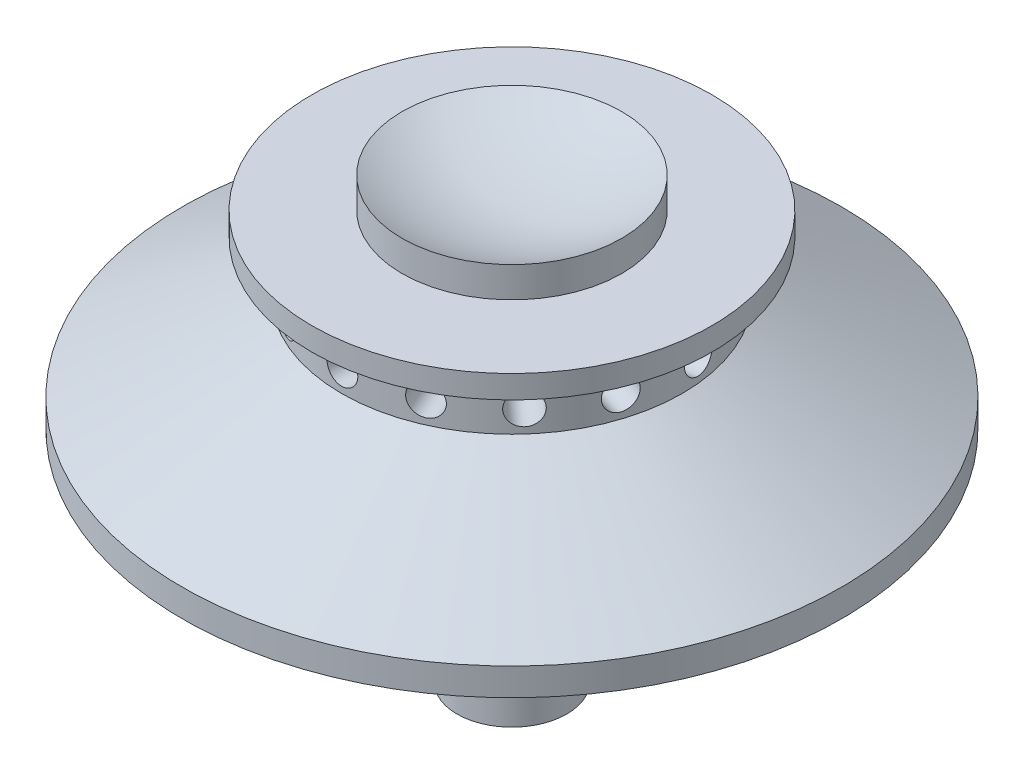
SolidWorks part; units mm, degrees
material "3003 Alloy"
ref_plane "Front Plane" through (0, 0, 0) normal (0, 0, 1) x (1, 0, 0)
ref_plane "Top Plane" through (0, 0, 0) normal (0, 1, 0) x (1, 0, 0)
ref_plane "Right Plane" through (0, 0, 0) normal (1, 0, 0) x (0, 0, -1)
sketch "Sketch1" plane through (0, 0, 0) normal (0, 0, 1) x (1, 0, 0)
  line L0 (0, 0) -> (-38.1, 0)
  line L1 (-38.1, 0) -> (-38.1, 3.175)
  line L2 (0, 0) -> (0, 22.225)
  line L3 (-12.7, 21.8741) -> (-12.7, 25.4)
  line L4 (-12.7, 21.8741) -> (-23.1308, 21.8741)
  line L5 (-23.1308, 21.8741) -> (-23.1308, 19.2253)
  line L6 (-23.1308, 19.2253) -> (-19.683, 19.2253)
  line L7 (-19.683, 19.2253) -> (-19.683, 13.3554)
  line L8 (-19.683, 13.3554) -> (-38.1, 3.175)
  line L9 (0, 22.225) -> (13.4343, 22.225) construction
  line L10 (0, 22.225) -> (0, 49.2125) construction
  arc A0 (0, 22.225) -> (-12.7, 25.4) centre (0, 49.2125) cw
  dimension "D6" = 22.225
  dimension "D1" = 76.2
  dimension "D4" = 25.4
  dimension "D5" = 3.175
  dimension "D7" = 25.4
revolve "Revolve1" add sketch "Sketch1" angle 360 about L10
hole_wizard "9/64 (0.14063) Diameter Hole1" positions "3DSketch1" profile "Sketch2" hole size "9/64" standard "Ansi Inch"
sketch3d "3DSketch1"
  point P0 (0, 15.875, 19.683)
  dimension "D1" = 15.875
sketch "Sketch2" plane through (0, 15.875, 19.683) normal (1, 0, 0) x (0, -1, 0)
  line L0 (0, 0) -> (0, 13.7731)
  line L1 (0, 13.7731) -> (1.786, 12.7)
  line L2 (1.786, 12.7) -> (1.786, 0)
  line L5 (1.786, 0) -> (0, 0)
  line L10 (0, 13.7731) -> (-1.786, 12.7) construction
  line L11 (0, -6.35) -> (0, 107.95) construction
  dimension "Hole Dia." = 3.572
  dimension "Hole Depth" = 12.7
  dimension "Drill Angle" = 118
pattern_circular "CirPattern1" count 15 over 360 about axis through (0, 22.225, 0) along (0, 1, 0) of "9/64 (0.14063) Diameter Hole1"
sketch "Sketch3" plane through (0, 0, 0) normal (0, -1, 0) x (1, 0, 0)
  circle A0 centre (0, 0) radius 6.35
  dimension "D1" = 12.7
extrude "Extrude1" add sketch "Sketch3" along normal blind 25.4
